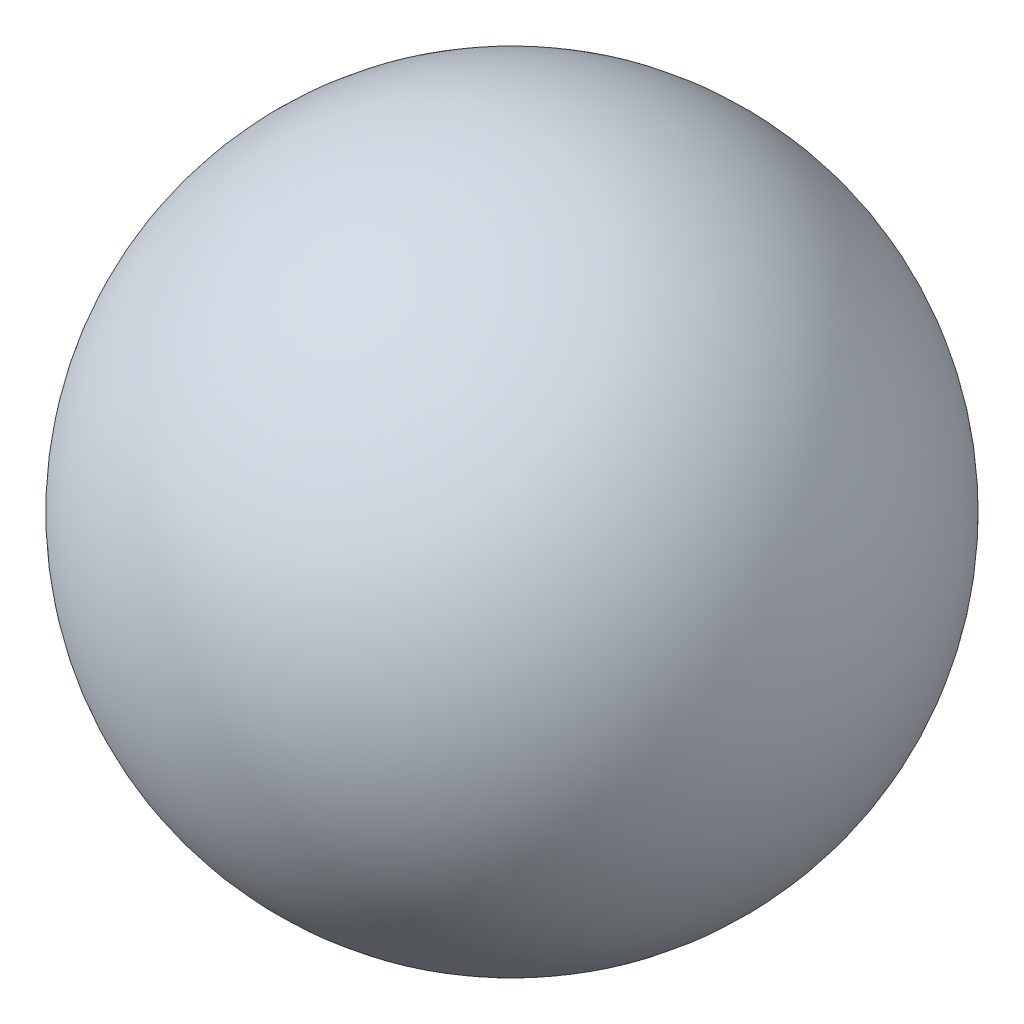
SolidWorks part; units mm, degrees
ref_plane "Front" through (0, 0, 0) normal (0, 0, 1) x (1, 0, 0)
ref_plane "Top" through (0, 0, 0) normal (0, 1, 0) x (1, 0, 0)
ref_plane "Right" through (0, 0, 0) normal (1, 0, 0) x (0, 0, -1)
sketch "Skizze1" plane through (0, 0, 0) normal (0, 0, 1) x (1, 0, 0)
  line L0 (0, -10) -> (0, 10)
  arc A0 (0, -10) -> (0, 10) centre (0, 0) ccw
  dimension "D1" = 10
revolve "Rotation1" add sketch "Skizze1" angle 360 about L0
